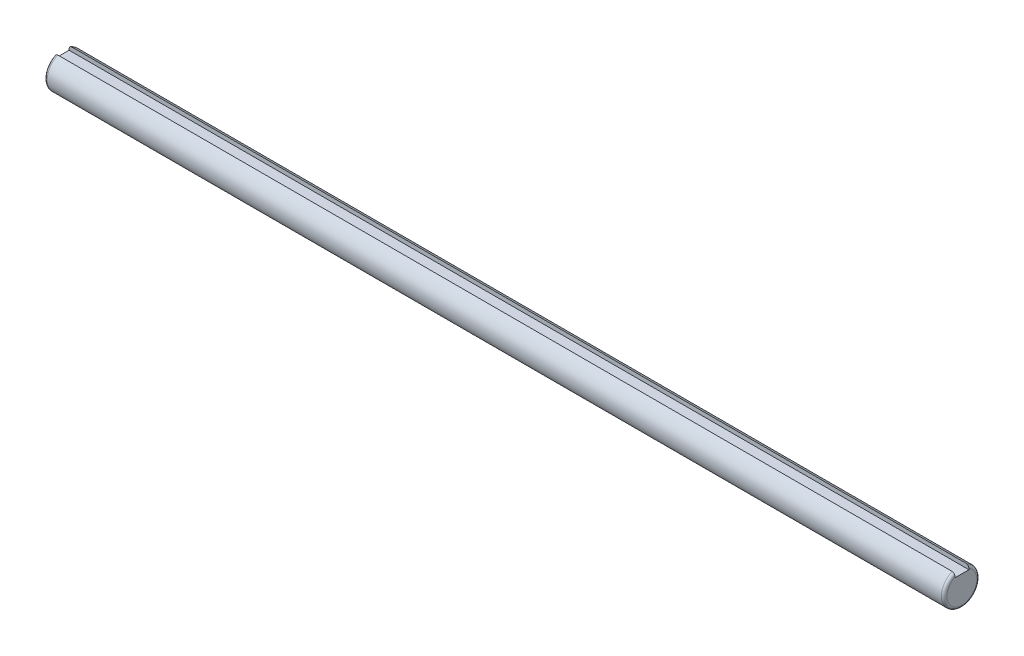
SolidWorks part; units mm, degrees
ref_plane "Front Plane" through (0, 0, 0) normal (0, 0, 1) x (1, 0, 0)
ref_plane "Top Plane" through (0, 0, 0) normal (0, 1, 0) x (1, 0, 0)
ref_plane "Right Plane" through (0, 0, 0) normal (1, 0, 0) x (0, 0, -1)
sketch "Sketch2" plane through (0, 0, 0) normal (1, 0, 0) x (0, 0, -1)
  line L2 (2.5, 5.8372) -> (2.5, 4.35)
  line L3 (2.5, 4.35) -> (-2.5, 4.35)
  line L4 (-2.5, 5.8372) -> (-2.5, 4.35)
  arc A0 (-2.5, 5.8372) -> (2.5, 5.8372) centre (0, 0) ccw
  point P3 (0, 6.35)
  dimension "D1" = 12.7
  dimension "D2" = 5
extrude "Boss-Extrude1" add sketch "Sketch2" along normal blind 322.5
fillet "Fillet1" radius 1 2 edges at (0, -6.35, 0) (322.5, -6.35, 0)
